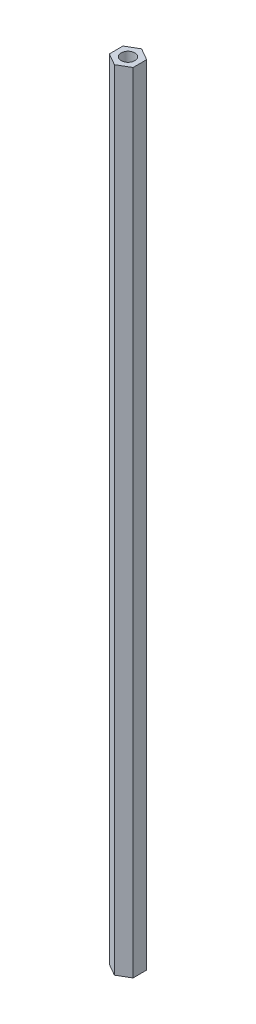
SolidWorks part; units mm, degrees
ref_plane "Face" through (0, 0, 0) normal (0, 0, 1) x (1, 0, 0)
ref_plane "Dessus" through (0, 0, 0) normal (0, 1, 0) x (1, 0, 0)
ref_plane "Droite" through (0, 0, 0) normal (1, 0, 0) x (0, 0, -1)
sketch "Esquisse1" plane through (0, 0, 0) normal (0, 1, 0) x (1, 0, 0)
  line L0 (0, 0) -> (0, 5.5688) construction
  line L1 (0, 5) -> (-4.3301, 2.5)
  line L2 (-4.3301, 2.5) -> (-4.3301, -2.5)
  line L3 (-4.3301, -2.5) -> (0, -5)
  line L4 (0, -5) -> (4.3301, -2.5)
  line L5 (4.3301, -2.5) -> (4.3301, 2.5)
  line L6 (4.3301, 2.5) -> (0, 5)
  circle A0 centre (0, 0) radius 4.3301 construction
  circle A1 centre (0, 0) radius 2.5
  dimension "D1" = 10
  dimension "D2" = 5
extrude "Extrusion1" add sketch "Esquisse1" along normal blind 289
